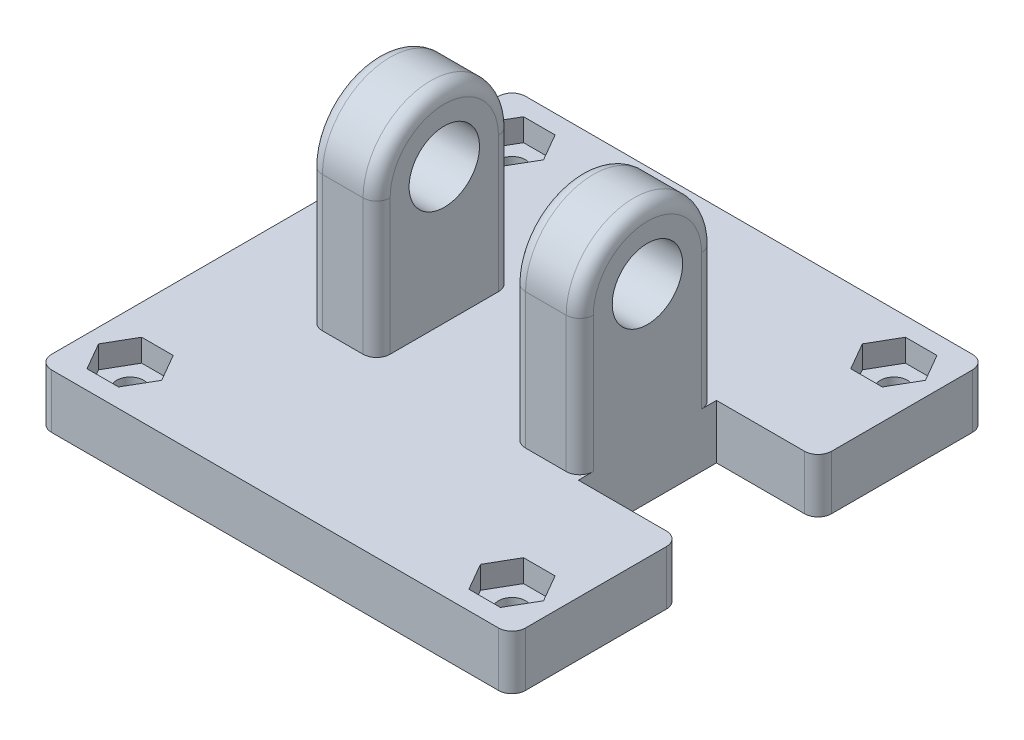
SolidWorks part; units mm, degrees
ref_plane "Plan de face" through (0, 0, 0) normal (0, 0, 1) x (1, 0, 0)
ref_plane "Plan de dessus" through (0, 0, 0) normal (0, 1, 0) x (1, 0, 0)
ref_plane "Plan de droite" through (0, 0, 0) normal (1, 0, 0) x (0, 0, -1)
sketch "Esquisse2" plane through (0, 0, 0) normal (1, 0, 0) x (0, 0, -1)
  line L0 (5, 0) -> (5, -10)
  line L2 (-5, 0) -> (-5, -10)
  line L3 (-5, -10) -> (5, -10)
  circle A0 centre (0, 0) radius 2.6
  arc A2 (5, 0) -> (-5, 0) centre (0, 0) ccw
  dimension "D1" = 5.2
  dimension "D2" = 10
  dimension "D3" = 5
  dimension "D4" = 5
extrude "Boss.-Extru.1" add sketch "Esquisse2" along normal mid plane 20
sketch "Esquisse4" plane through (0, -10, 0) normal (0, -1, 0) x (1, 0, 0)
  line L1 (-17.5, -17.5) -> (17.5, -17.5)
  line L2 (-17.5, -17.5) -> (-17.5, 17.5)
  line L3 (-17.5, 17.5) -> (17.5, 17.5)
  line L4 (17.5, -17.5) -> (17.5, 17.5)
  dimension "D1" = 35
  dimension "D2" = 35
  dimension "D3" = 17.5
  dimension "D4" = 17.5
extrude "Boss.-Extru.2" add sketch "Esquisse4" along normal blind 4
sketch "Esquisse5" plane through (0, -10, 0) normal (0, 1, 0) x (1, 0, 0)
  circle A0 centre (14.1, -14.1) radius 1
  circle A1 centre (14.1, 14.1) radius 1
  circle A2 centre (-14.1, 14.1) radius 1
  circle A3 centre (-14.1, -14.1) radius 1
  point P15 (0, 0)
  dimension "D1" = 2
  dimension "D2" = 28.2
  dimension "D3" = 28.2
  dimension "D4" = 14.1
  dimension "D5" = 14.1
extrude "Enlèv. mat.-Extru.1" cut sketch "Esquisse5" against normal up to next contours A0
sketch "Esquisse6" plane through (0, 0, 5) normal (0, 0, 1) x (1, 0, 0)
  line L0 (10, -10) -> (-10, -10) construction
  line L1 (-5, 6.1864) -> (5, 6.1864)
  line L2 (-5, 6.1864) -> (-5, -10)
  line L3 (-5, -10) -> (5, -10)
  line L4 (5, 6.1864) -> (5, -10)
  dimension "D1" = 5
  dimension "D2" = 10
extrude "Enlèv. mat.-Extru.2" cut sketch "Esquisse6" against normal through all
sketch "Esquisse7" plane through (0, -10, 0) normal (0, 1, 0) x (1, 0, 0)
  line L8 (-11.77, -14.1) -> (-12.935, -12.0822)
  line L9 (-12.935, -12.0822) -> (-15.265, -12.0822)
  line L10 (-15.265, -12.0822) -> (-16.43, -14.1)
  line L11 (-16.43, -14.1) -> (-15.265, -16.1178)
  line L12 (-15.265, -16.1178) -> (-12.935, -16.1178)
  line L13 (-12.935, -16.1178) -> (-11.77, -14.1)
  line L14 (16.43, -14.1) -> (15.265, -12.0822)
  line L15 (15.265, -12.0822) -> (12.935, -12.0822)
  line L16 (12.935, -12.0822) -> (11.77, -14.1)
  line L17 (11.77, -14.1) -> (12.935, -16.1178)
  line L18 (12.935, -16.1178) -> (15.265, -16.1178)
  line L19 (15.265, -16.1178) -> (16.43, -14.1)
  line L20 (16.43, 14.1) -> (15.265, 16.1178)
  line L21 (15.265, 16.1178) -> (12.935, 16.1178)
  line L22 (12.935, 16.1178) -> (11.77, 14.1)
  line L23 (11.77, 14.1) -> (12.935, 12.0822)
  line L24 (12.935, 12.0822) -> (15.265, 12.0822)
  line L25 (15.265, 12.0822) -> (16.43, 14.1)
  line L26 (-11.77, 14.1) -> (-12.935, 16.1178)
  line L27 (-12.935, 16.1178) -> (-15.265, 16.1178)
  line L28 (-15.265, 16.1178) -> (-16.43, 14.1)
  line L29 (-16.43, 14.1) -> (-15.265, 12.0822)
  line L30 (-15.265, 12.0822) -> (-12.935, 12.0822)
  line L31 (-12.935, 12.0822) -> (-11.77, 14.1)
  line L32 (-17.5, 17.5) -> (17.5, 17.5) construction
  line L33 (17.5, -17.5) -> (-17.5, -17.5) construction
  circle A5 centre (-14.1, -14.1) radius 2.0178 construction
  circle A6 centre (14.1, -14.1) radius 2.0178 construction
  circle A7 centre (14.1, 14.1) radius 2.0178 construction
  circle A8 centre (-14.1, 14.1) radius 2.0178 construction
  dimension "D1" = 2.33
  dimension "D2" = 2.33
  dimension "D3" = 2.33
  dimension "D4" = 2.33
extrude "Enlèv. mat.-Extru.3" cut sketch "Esquisse7" against normal blind 1.66
sketch "Esquisse8" plane through (0, -10, 0) normal (0, 1, 0) x (1, 0, 0)
  line L10 (17.5, 17.5) -> (17.5, -17.5) construction
  line L11 (17.5, 5.1) -> (10, 5.1)
  line L12 (17.5, 5.1) -> (17.5, -5.1)
  line L13 (17.5, -5.1) -> (10, -5.1)
  line L14 (10, 5.1) -> (10, -5.1)
  line L15 (10, -5) -> (10, 5) construction
  point P2 (0, 0)
  dimension "D1" = 10.2
  dimension "D2" = 5.1
extrude "Enlèv. mat.-Extru.4" cut sketch "Esquisse8" against normal up to next
fillet "Congé1" radius 1 18 edges at (5, -5, -5) (5, -5, 5) (-5, -5, 5) (-5, -5, -5) (10, -5, -5) (10, -5, 5) (-10, -5, -5) (-10, -5, 5) (5, 5, 0) (-5, 5, 0) (10, 5, 0) (-10, 5, 0) (-17.5, -12, -17.5) (-17.5, -12, 17.5) (17.5, -12, -17.5) (17.5, -12, 17.5) (17.5, -12, 5.1) (17.5, -12, -5.1)
